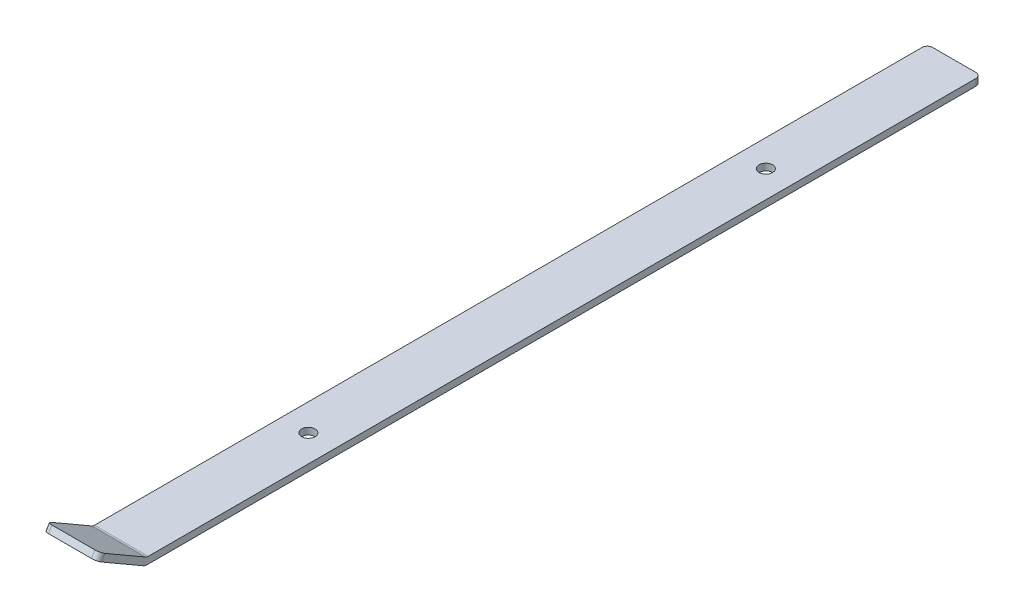
SolidWorks part; units mm, degrees
material "1023 Carbon Steel Sheet (SS)"
ref_plane "Front" through (0, 0, 0) normal (0, 0, 1) x (1, 0, 0)
ref_plane "Top" through (0, 0, 0) normal (0, 1, 0) x (1, 0, 0)
ref_plane "Right" through (0, 0, 0) normal (1, 0, 0) x (0, 0, -1)
sketch "Sketch1" plane through (0, 0, 0) normal (1, 0, 0) x (0, 0, -1)
  line L0 (0, 0) -> (-21.997, 12.7)
  line L1 (0, 0) -> (393.7, 0)
  line L2 (0, 0) -> (0, -3.175) construction
  line L3 (0, -3.175) -> (393.7, -3.175)
  line L4 (393.7, 0) -> (393.7, -3.175)
  line L5 (-21.997, 12.7) -> (-23.5845, 9.9504)
  line L6 (-23.5845, 9.9504) -> (-1.5875, -2.7496)
  arc A0 (0, -3.175) -> (-1.5875, -2.7496) centre (0, 0) cw
  dimension "D1" = 150
  dimension "D2" = 25.4
  dimension "D3" = 393.7
  dimension "D4" = 3.175
extrude "Boss-Extrude1" add sketch "Sketch1" along normal blind 25.4
sketch "Sketch2" plane through (0, 0, 0) normal (0, 1, 0) x (1, 0, 0)
  line L0 (12.7, 0) -> (12.7, 19.1815) construction
  line L2 (25.4, 0) -> (0, 0) construction
  line L3 (25.4, 393.7) -> (0, 393.7) construction
  circle A0 centre (12.7, 88.9) radius 3.175
  circle A1 centre (12.7, 304.8) radius 3.175
  point P3 (12.7, 0)
  dimension "D1" = 6.35
  dimension "D2" = 88.9
  dimension "D3" = 88.9
extrude "Cut-Extrude1" cut sketch "Sketch2" against normal through all
fillet "Fillet1" radius 2.54 5 edges at (0, -1.5875, -393.7) (25.4, -1.5875, -393.7) (0, 11.3252, 22.7908) (25.4, 11.3252, 22.7908) (12.7, 0, 0)
equation "\"12ion\"=3.48165"
